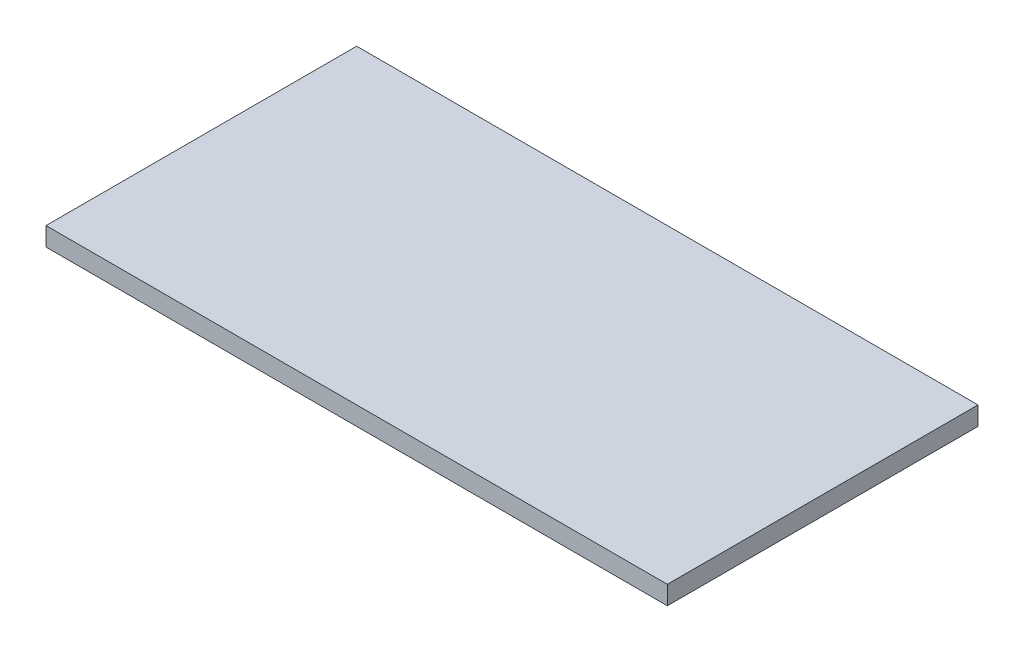
SolidWorks part; units mm, degrees
ref_plane "Front Plane" through (0, 0, 0) normal (0, 0, 1) x (1, 0, 0)
ref_plane "Top Plane" through (0, 0, 0) normal (0, 1, 0) x (1, 0, 0)
ref_plane "Right Plane" through (0, 0, 0) normal (1, 0, 0) x (0, 0, -1)
sketch "Sketch1" plane through (0, 0, 0) normal (0, 1, 0) x (1, 0, 0)
  line L1 (-12.7, -6.35) -> (12.7, -6.35)
  line L2 (-12.7, -6.35) -> (-12.7, 6.35)
  line L3 (-12.7, 6.35) -> (12.7, 6.35)
  line L4 (12.7, -6.35) -> (12.7, 6.35)
  line L5 (-12.7, -6.35) -> (12.7, 6.35) construction
  line L6 (-12.7, 6.35) -> (12.7, -6.35) construction
  point P0 (0, 0)
  dimension "D1" = 12.7
  dimension "D2" = 25.4
extrude "Boss-Extrude1" add sketch "Sketch1" along normal blind 0.762
